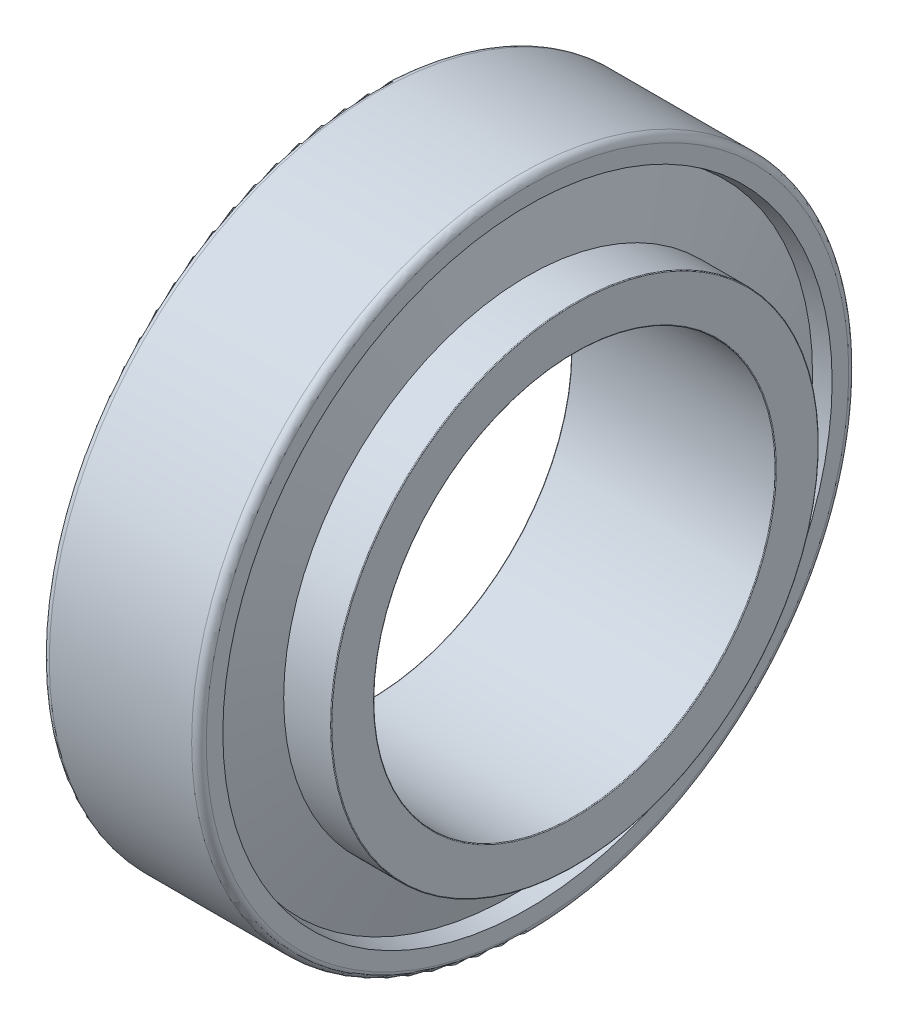
SolidWorks part; units mm, degrees
material "AISI Тип A2 Инструментальная сталь"
ref_plane "Спереди" through (0, 0, 0) normal (0, 0, 1) x (1, 0, 0)
ref_plane "Сверху" through (0, 0, 0) normal (0, 1, 0) x (1, 0, 0)
ref_plane "Справа" through (0, 0, 0) normal (1, 0, 0) x (0, 0, -1)
sketch "Эскиз1" plane through (0, 0, 0) normal (0, 0, 1) x (1, 0, 0)
  line L20 (-882.5277, 0) -> (43243.8573, 0) construction
  line L33 (5.6738, 75.7371) -> (0, 74.5635)
  line L34 (0, 74.5635) -> (0, 88)
  line L35 (2, 90) -> (41, 90)
  line L36 (43, 88) -> (43, 83.4579)
  line L37 (43, 83.4579) -> (38.552, 82.5378)
  line L38 (5.6738, 75.7371) -> (38.552, 82.5378) construction
  line L39 (11.3477, 55.3929) -> (0, 55.3929)
  line L40 (0, 55.3929) -> (0, 55.2)
  line L41 (0.2, 55) -> (55.8, 55)
  line L42 (56, 55.2) -> (56, 66.5892)
  line L43 (55.8, 66.7892) -> (43, 66.7892)
  line L44 (43, 66.7892) -> (43, 66.5892)
  line L45 (11.3477, 55.3929) -> (43, 66.5892) construction
  line L46 (43, 66.5892) -> (38.552, 82.5378)
  line L47 (11.3477, 55.3929) -> (5.6738, 75.7371)
  line L48 (8.5108, 65.565) -> (40.776, 74.5635) construction
  line L49 (0, 74.5635) -> (40.776, 74.5635) construction
  line L50 (5.6738, 75.7371) -> (5.6738, 55.3929) construction
  arc A0 (0, 88) -> (2, 90) centre (2, 88) cw
  arc A1 (41, 90) -> (43, 88) centre (41, 88) cw
  arc A2 (0, 55.2) -> (0.2, 55) centre (0.2, 55.2) ccw
  arc A3 (56, 55.2) -> (55.8, 55) centre (55.8, 55.2) cw
  arc A4 (55.8, 66.7892) -> (56, 66.5892) centre (55.8, 66.5892) cw
  point P12 (40.776, 74.5635)
  dimension "гост r1" = 0.2
  dimension "гост r2" = 2
  dimension "гост DD" = 180
  dimension "гост B" = 56
  dimension "гост C" = 43
  dimension "гост T" = 56
  dimension "гост E" = 149.127
  dimension "гост d" = 110
  dimension "гост alfa" = 15.583
revolve "Повернуть1" add sketch "Эскиз1" angle 360 about L20
